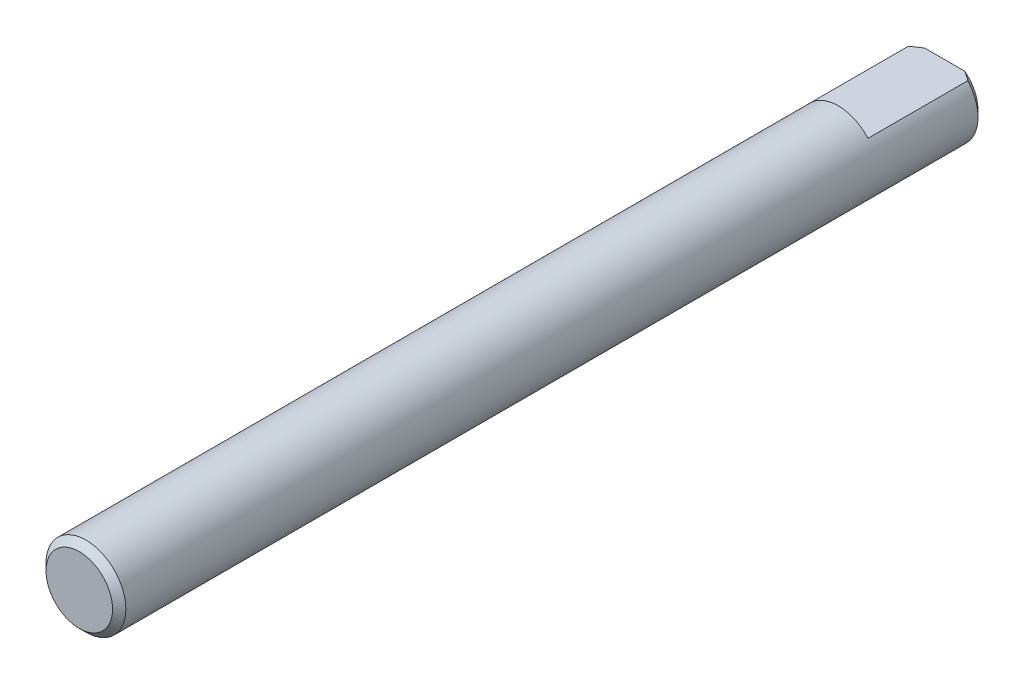
SolidWorks part; units mm, degrees
ref_plane "Front Plane" through (0, 0, 0) normal (0, 0, 1) x (1, 0, 0)
ref_plane "Top Plane" through (0, 0, 0) normal (0, 1, 0) x (1, 0, 0)
ref_plane "Right Plane" through (0, 0, 0) normal (1, 0, 0) x (0, 0, -1)
sketch "Sketch1" plane through (0, 0, 0) normal (0, 0, 1) x (1, 0, 0)
  circle A0 centre (0, 0) radius 3
  dimension "D1" = 6
extrude "Boss-Extrude1" add sketch "Sketch1" along normal mid plane 65
sketch "Sketch2" plane through (0, 0, -32.5) normal (0, 0, -1) x (-1, 0, 0)
  line L0 (-2.2361, 2) -> (2.2361, 2)
  circle A1 centre (0, 0) radius 3
  arc A2 (2.2361, 2) -> (-2.2361, 2) centre (0, 0) ccw
  dimension "D2" = 2
  dimension "D1" = 0
extrude "Cut-Extrude1" cut sketch "Sketch2" against normal blind 8
chamfer "Chamfer1" distance 0.5 angle 45 2 edges at (3, 0, 32.5) (0, -3, -32.5)
